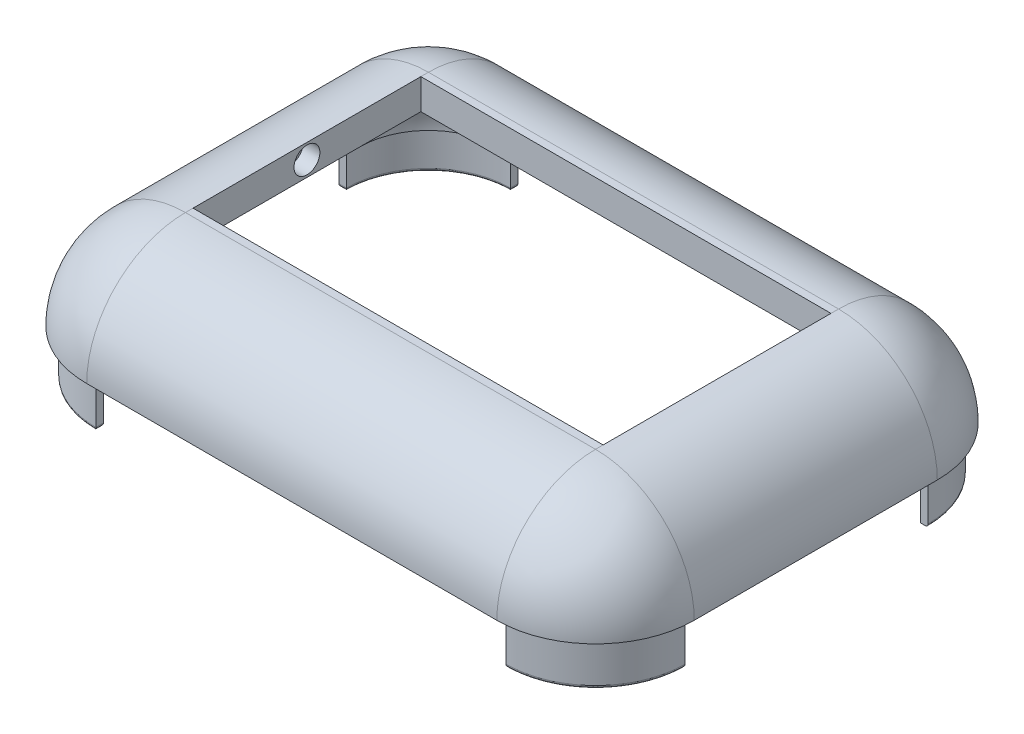
SolidWorks part; units mm, degrees
material "ABS"
ref_plane "Front Plane" through (0, 0, 0) normal (0, 0, 1) x (1, 0, 0)
ref_plane "Top Plane" through (0, 0, 0) normal (0, 1, 0) x (1, 0, 0)
ref_plane "Right Plane" through (0, 0, 0) normal (1, 0, 0) x (0, 0, -1)
sketch "Sketch1" plane through (0, 0, 0) normal (0, 1, 0) x (1, 0, 0)
  line L1 (-20, 14.5) -> (20, 14.5)
  line L2 (-20, 14.5) -> (-20, -14.5)
  line L3 (-20, -14.5) -> (20, -14.5)
  line L4 (20, 14.5) -> (20, -14.5)
  line L5 (0, -14.5) -> (0, 14.5) construction
  line L6 (-20, 0) -> (20, 0) construction
  point P0 (0, 0)
  dimension "D1" = 29
  dimension "D2" = 40
extrude "Boss-Extrude1" add sketch "Sketch1" along normal blind 20
fillet "Fillet2" radius 6.5 12 edges at (0, 20, 14.5) (-20, 20, 0) (0, 20, -14.5) (20, 20, 0) (0, 0, -14.5) (-20, 0, 0) (0, 0, 14.5) (20, 0, 0) (20, 10, 14.5) (20, 10, -14.5) (-20, 10, -14.5) (-20, 10, 14.5)
ref_plane "Plane2" through (0, 13.5, 0) normal (0, 1, 0) x (1, 0, 0)
sketch "Sketch3" plane through (0, 13.5, 0) normal (0, 1, 0) x (1, 0, 0)
  line L1 (24.4913, 19.6546) -> (-24.4913, 19.6546)
  line L2 (24.4913, 19.6546) -> (24.4913, -19.6546)
  line L3 (24.4913, -19.6546) -> (-24.4913, -19.6546)
  line L4 (-24.4913, 19.6546) -> (-24.4913, -19.6546)
  line L5 (0, -19.6546) -> (0, 19.6546) construction
  line L6 (24.4913, 0) -> (-24.4913, 0) construction
  point P0 (0, 0)
extrude "Cut-Extrude1" cut sketch "Sketch3" against normal through all
shell "Shell1" thickness 2
sketch "Sketch5" plane through (0, 13.5, 0) normal (0, -1, 0) x (1, 0, 0)
  line L0 (-13.5, 13.9) -> (-13.5, 13.4)
  line L1 (-19.4, 8) -> (-18.9, 8)
  line L2 (-19.4, -8) -> (-18.9, -8)
  line L3 (-13.5, -13.4) -> (-13.5, -13.9)
  line L4 (0, -3.575) -> (0, 3.575) construction
  line L5 (13.5, -13.4) -> (13.5, -13.9)
  line L6 (19.4, -8) -> (18.9, -8)
  line L7 (19.4, 8) -> (18.9, 8)
  line L8 (19.4, -8) -> (19.4, 8)
  line L9 (13.5, 13.9) -> (-13.5, 13.9)
  line L10 (-19.4, 8) -> (-19.4, -8)
  line L11 (-13.5, -13.9) -> (13.5, -13.9)
  line L12 (13.5, 13.9) -> (13.5, 13.4)
  arc A4 (13.5, -13.4) -> (18.9, -8) centre (13.5, -8) ccw
  arc A5 (18.9, 8) -> (13.5, 13.4) centre (13.5, 8) ccw
  arc A6 (-18.9, -8) -> (-13.5, -13.4) centre (-13.5, -8) ccw
  arc A7 (-13.5, 13.4) -> (-18.9, 8) centre (-13.5, 8) ccw
  arc A8 (19.4, 8) -> (13.5, 13.9) centre (13.5, 8) ccw
  arc A9 (-13.5, 13.9) -> (-19.4, 8) centre (-13.5, 8) ccw
  arc A10 (-19.4, -8) -> (-13.5, -13.9) centre (-13.5, -8) ccw
  arc A11 (13.5, -13.9) -> (19.4, -8) centre (13.5, -8) ccw
  arc A12 (19.4, 8) -> (13.5, 13.9) centre (13.5, 8) ccw
  arc A13 (-13.5, 13.9) -> (-19.4, 8) centre (-13.5, 8) ccw
  arc A14 (-19.4, -8) -> (-13.5, -13.9) centre (-13.5, -8) ccw
  arc A15 (13.5, -13.9) -> (19.4, -8) centre (13.5, -8) ccw
  dimension "D1" = 0.6
  dimension "D2" = 0.5
extrude "Boss-Extrude3" add sketch "Sketch5" along normal blind 3
fillet "Fillet3" radius 0.2 13 edges at (-17.3184, 10.5, 11.8184) (-17.6719, 10.5, 12.1719) (-17.3184, 10.5, -11.8184) (-17.6719, 10.5, -12.1719) (17.3184, 10.5, 11.8184) (17.6719, 10.5, 12.1719) (17.6719, 10.5, -12.1719) (-19.15, 10.5, 8) (-13.5, 10.5, 13.65) (-13.5, 10.5, -13.65) (-19.15, 10.5, -8) (13.5, 10.5, 13.65) (19.15, 10.5, 8)
sketch "Sketch6" plane through (0, 20, 0) normal (0, 1, 0) x (1, 0, 0)
  line L1 (-13.5, 7.5) -> (13.5, 7.5)
  line L2 (-13.5, 7.5) -> (-13.5, -7.5)
  line L3 (-13.5, -7.5) -> (13.5, -7.5)
  line L4 (13.5, 7.5) -> (13.5, -7.5)
  line L5 (0, -7.5) -> (0, 7.5) construction
  line L6 (-13.5, 0) -> (13.5, 0) construction
  point P0 (0, 0)
  dimension "D1" = 27
  dimension "D2" = 15
extrude "Cut-Extrude2" cut sketch "Sketch6" against normal through all
sketch "Sketch7" plane through (-13.5, 0, 0) normal (1, 0, 0) x (0, 0, -1)
  line L0 (-7.5, 19) -> (7.5, 19) construction
  line L1 (-7.5, 18) -> (-7.5, 20) construction
  line L2 (7.5, 18) -> (7.5, 20) construction
  circle A0 centre (0, 19) radius 0.85
  dimension "D1" = 1.7
extrude "Cut-Extrude3" cut sketch "Sketch7" against normal blind 1.1
sketch "Sketch9" plane through (13.5, 0, 0) normal (-1, 0, 0) x (0, 0, 1)
  line L0 (0.85, 19) -> (0.85, 18)
  line L1 (7.5, 18) -> (-7.5, 18) construction
  line L3 (-0.85, 18) -> (-0.85, 19)
  line L4 (-0.85, 18) -> (-0.85, 17.3682)
  line L5 (-0.85, 17.3682) -> (0.85, 17.3682)
  line L6 (0.85, 17.3682) -> (0.85, 18)
  arc A0 (0.85, 19) -> (-0.85, 19) centre (0, 19) ccw
  dimension "D1" = 1.7
  dimension "D2" = 1.6318
extrude "Cut-Extrude4" cut sketch "Sketch9" against normal blind 1
